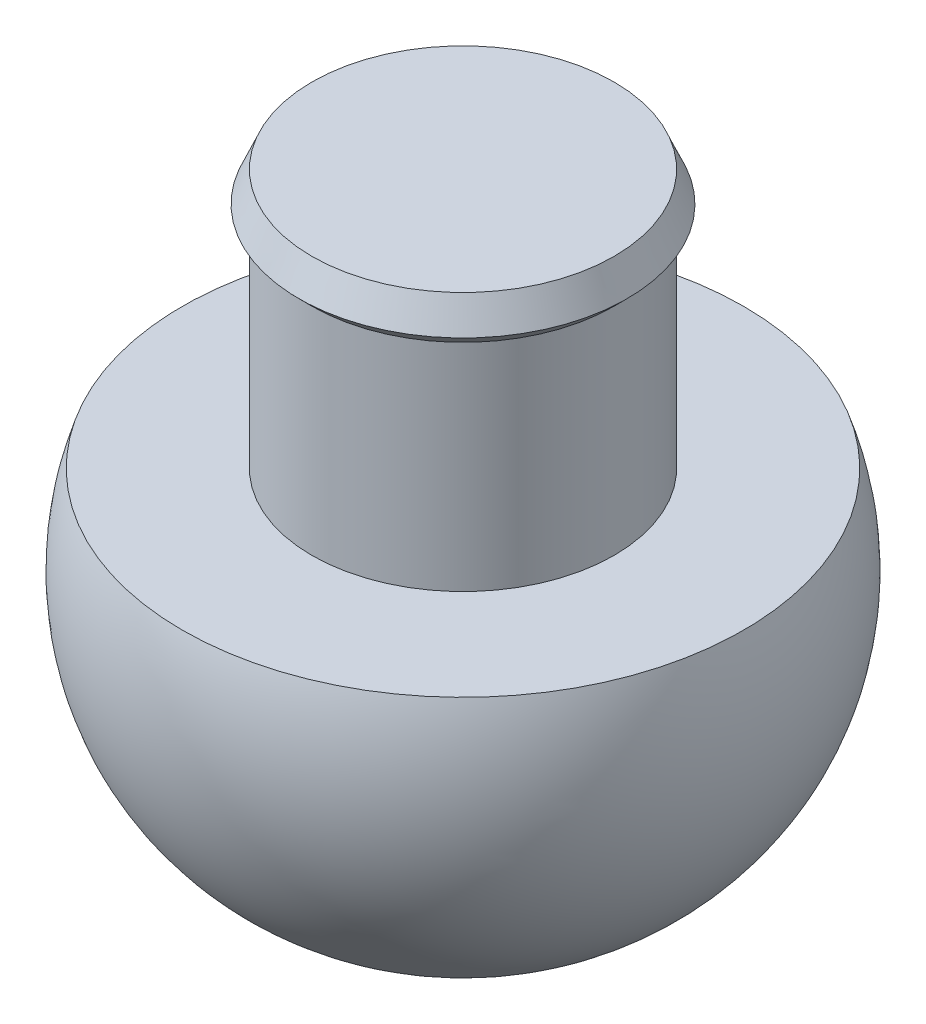
SolidWorks part; units mm, degrees
ref_plane "Front Plane" through (0, 0, 0) normal (0, 0, 1) x (1, 0, 0)
ref_plane "Top Plane" through (0, 0, 0) normal (0, 1, 0) x (1, 0, 0)
ref_plane "Right Plane" through (0, 0, 0) normal (1, 0, 0) x (0, 0, -1)
sketch "Sketch1" plane through (0, 0, 0) normal (0, 0, 1) x (1, 0, 0)
  line L1 (-3.5, 1.6099) -> (-3.5, -3.3901)
  line L2 (0, 5.1461) -> (0, -13.6974) construction
  line L3 (0, -11.8974) -> (0, 2.6099)
  line L4 (-3.5, 1.6099) -> (-3.8, 1.9099)
  line L5 (-3.8, 1.9099) -> (-3.5, 2.6099)
  line L6 (-3.5, 2.6099) -> (0, 2.6099)
  line L7 (-3.5, 0.5821) -> (-3.5, 2.5143) construction
  line L8 (-3.5, -3.3901) -> (-6.5, -3.3901)
  line L9 (-3.8, 1.9099) -> (-3.5, 1.9099) construction
  arc A0 (-6.5, -3.3901) -> (0, -11.8974) centre (-0.3625, -5.4376) ccw
  dimension "D3" = 0.3
  dimension "D4" = 1
  dimension "D5" = 3
  dimension "D1" = 5
  dimension "D2" = 3.5
  dimension "D6" = 0.3
revolve "Revolve2" add sketch "Sketch1" angle 360 about L3
